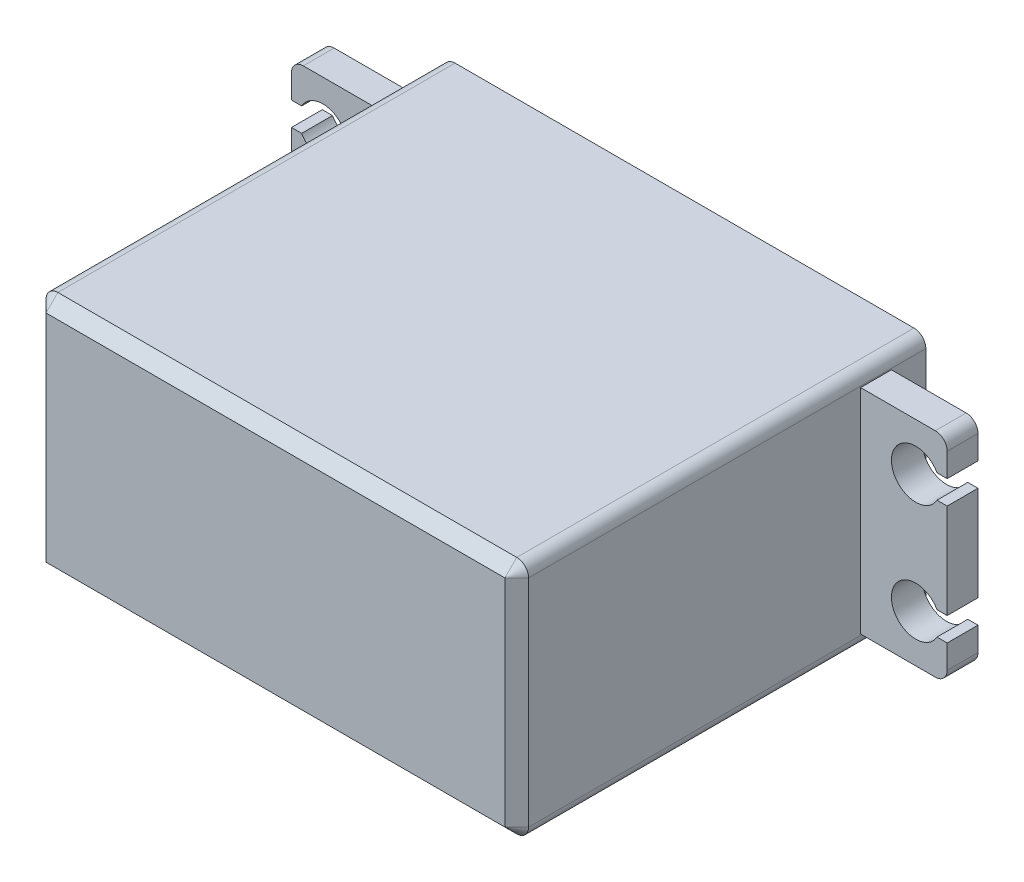
SolidWorks part; units mm, degrees
ref_plane "Front Plane" through (0, 0, 0) normal (0, 0, 1) x (1, 0, 0)
ref_plane "Top Plane" through (0, 0, 0) normal (0, 1, 0) x (1, 0, 0)
ref_plane "Right Plane" through (0, 0, 0) normal (1, 0, 0) x (0, 0, -1)
sketch "Sketch1" plane through (0, 0, 0) normal (0, 0, 1) x (1, 0, 0)
  line L1 (-20.35, 10.1) -> (20.35, 10.1)
  line L2 (-20.35, 10.1) -> (-20.35, -10.1)
  line L3 (-20.35, -10.1) -> (20.35, -10.1)
  line L4 (20.35, 10.1) -> (20.35, -10.1)
  line L5 (-20.35, 10.1) -> (20.35, -10.1) construction
  line L6 (-20.35, -10.1) -> (20.35, 10.1) construction
  point P0 (0, 0)
  dimension "D1" = 20.2
  dimension "D2" = 40.7
extrude "Boss-Extrude1" add sketch "Sketch1" along normal blind 34.5
ref_plane "Plane1" through (0, 0, 5.5) normal (0, 0, 1) x (1, 0, 0)
sketch "Sketch2" plane through (0, 0, 5.5) normal (0, 0, 1) x (1, 0, 0)
  line L0 (-20.35, 0) -> (-27.65, 0) construction
  line L1 (-20.35, 10.1) -> (-20.35, -10.1) construction
  line L2 (-20.35, 9) -> (-27.65, 9)
  line L3 (-27.65, 9) -> (-27.65, 6)
  line L4 (-27.65, 6) -> (-26.7896, 6)
  line L5 (-27.65, -4) -> (-27.65, 4)
  line L6 (-27.65, 4) -> (-26.7896, 4)
  line L7 (-26.7896, 6) -> (-26.7896, 4) construction
  line L8 (-26.7896, 5) -> (-25, 5) construction
  line L9 (-20.35, 9) -> (-20.35, -9)
  line L10 (-26.7896, -5) -> (-25, -5) construction
  line L11 (-26.7896, -6) -> (-26.7896, -4) construction
  line L12 (-27.65, -4) -> (-26.7896, -4)
  line L13 (-27.65, -6) -> (-26.7896, -6)
  line L14 (-27.65, -9) -> (-27.65, -6)
  line L15 (-20.35, -9) -> (-27.65, -9)
  arc A0 (-26.7896, 6) -> (-26.7896, 4) centre (-25, 5) cw
  arc A1 (-26.7896, -6) -> (-26.7896, -4) centre (-25, -5) ccw
  dimension "D1" = 2.05
  dimension "D2" = 10
  dimension "D3" = 18
  dimension "D4" = 7.3
  dimension "D5" = 2
  dimension "D6" = 25
extrude "Boss-Extrude2" add sketch "Sketch2" against normal blind 2.6
fillet "Fillet2" radius 1 2 edges at (-27.65, -9, 4.2) (-27.65, 9, 4.2)
mirror "Mirror1" about plane through (0, 0, 0) normal (1, 0, 0) of "Boss-Extrude2", "Fillet2"
fillet "Fillet1" radius 1 4 edges at (-20.35, -10.1, 17.25) (20.35, -10.1, 17.25) (20.35, 10.1, 17.25) (-20.35, 10.1, 17.25)
chamfer "Chamfer1" distance 1 angle 45 8 edges at (-20.0571, 9.8071, 34.5) (0, 10.1, 34.5) (20.0571, 9.8071, 34.5) (20.35, 0, 34.5) (20.0571, -9.8071, 34.5) (0, -10.1, 34.5) (-20.0571, -9.8071, 34.5) (-20.35, 0, 34.5)
sketch "Sketch3" plane through (0, 0, 0) normal (0, 0, -1) x (-1, 0, 0)
  line L0 (20.35, -9) -> (20.35, 9) construction
  circle A0 centre (10.35, 0) radius 4
  dimension "D1" = 8
  dimension "D2" = 10
extrude "Boss-Extrude3" add sketch "Sketch3" along normal blind 3
